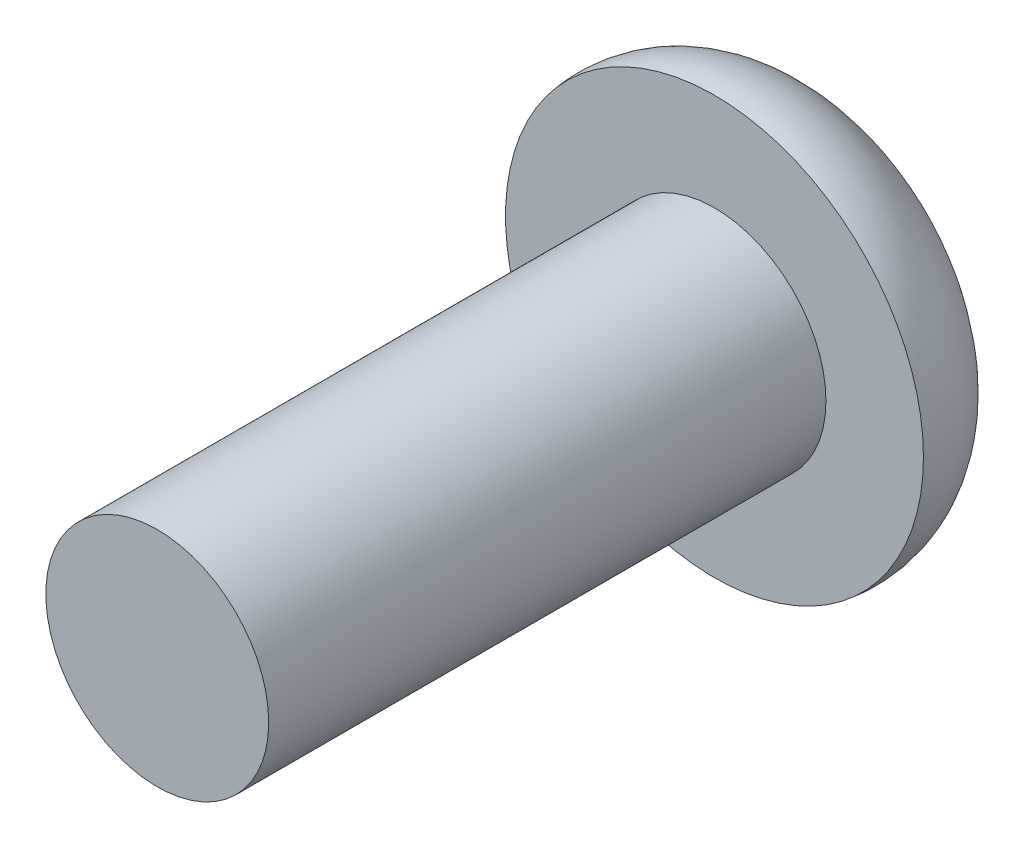
SolidWorks part; units mm, degrees
ref_plane "Front Plane" through (0, 0, 0) normal (0, 0, 1) x (1, 0, 0)
ref_plane "Top Plane" through (0, 0, 0) normal (0, 1, 0) x (1, 0, 0)
ref_plane "Right Plane" through (0, 0, 0) normal (1, 0, 0) x (0, 0, -1)
sketch "Sketch1" plane through (0, 0, 0) normal (0, 1, 0) x (1, 0, 0)
  line L0 (0, 0) -> (0, 12) construction
  line L1 (0, 0) -> (-2, 0)
  line L2 (-2, 0) -> (-2, 10)
  line L3 (-2, 10) -> (-3.75, 10)
  line L4 (-2, 12) -> (0, 12)
  line L5 (0, 0) -> (0, 12)
  arc A0 (-3.75, 10) -> (-2, 12) centre (-2, 10.2344) cw
  dimension "D5" = 2
  dimension "D1" = 2
  dimension "D2" = 3.75
  dimension "D3" = 2
  dimension "D4" = 10
revolve "Revolve1" add sketch "Sketch1" angle 360 about L0
sketch "Sketch2" plane through (0, 0, -12) normal (0, 0, -1) x (-1, 0, 0)
  line L1 (0, -1.4434) -> (1.25, -0.7217)
  line L2 (1.25, -0.7217) -> (1.25, 0.7217)
  line L3 (1.25, 0.7217) -> (0, 1.4434)
  line L4 (0, 1.4434) -> (-1.25, 0.7217)
  line L5 (-1.25, 0.7217) -> (-1.25, -0.7217)
  line L6 (-1.25, -0.7217) -> (0, -1.4434)
  circle A0 centre (0, 0) radius 1.25 construction
  dimension "D1" = 2.5
extrude "Cut-Extrude1" cut sketch "Sketch2" against normal blind 1.8
